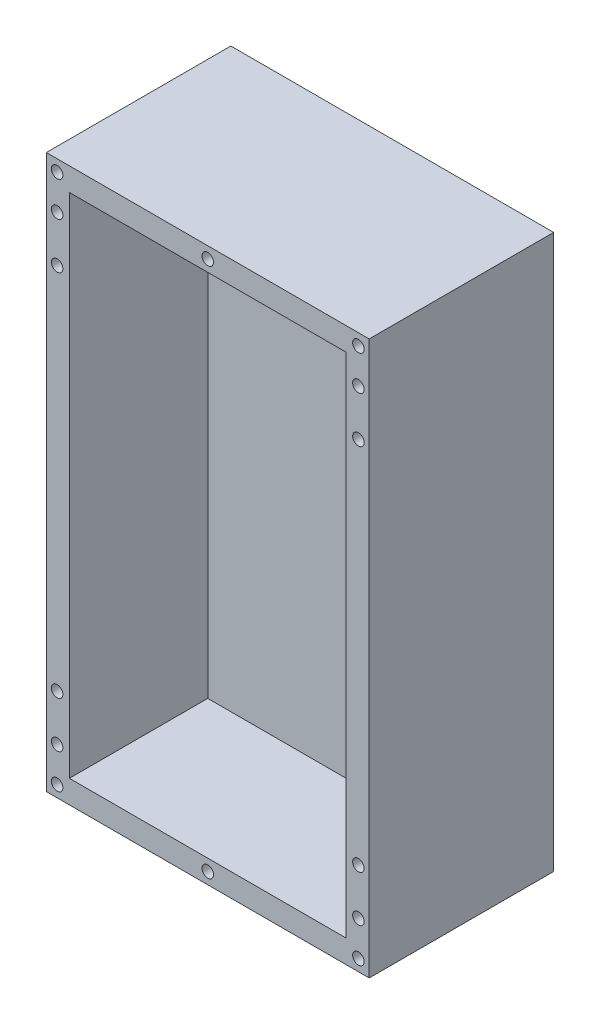
SolidWorks part; units mm, degrees
ref_plane "Front Plane" through (0, 0, 0) normal (0, 0, 1) x (1, 0, 0)
ref_plane "Top Plane" through (0, 0, 0) normal (0, 1, 0) x (1, 0, 0)
ref_plane "Right Plane" through (0, 0, 0) normal (1, 0, 0) x (0, 0, -1)
sketch "Sketch1" plane through (0, 0, 0) normal (0, 0, 1) x (1, 0, 0)
  line L0 (0, 609.6) -> (355.6, 0) construction
  line L1 (0, 609.6) -> (355.6, 609.6)
  line L2 (0, 609.6) -> (0, 0)
  line L3 (0, 0) -> (355.6, 0)
  line L4 (355.6, 609.6) -> (355.6, 0)
  line L5 (355.6, 609.6) -> (0, 0) construction
  line L9 (25.4, 584.2) -> (330.2, 584.2)
  line L10 (25.4, 584.2) -> (25.4, 25.4)
  line L11 (25.4, 25.4) -> (330.2, 25.4)
  line L12 (330.2, 584.2) -> (330.2, 25.4)
  line L13 (25.4, 584.2) -> (330.2, 25.4) construction
  line L14 (330.2, 584.2) -> (25.4, 25.4) construction
  point P12 (177.8, 304.8)
  point P13 (177.8, 304.8)
  dimension "D1" = 355.6
  dimension "D2" = 609.6
  dimension "D3" = 304.8
  dimension "D4" = 558.8
extrude "Boss-Extrude2" add sketch "Sketch1" along normal blind 203.2
ref_plane "Plane4" through (25.4, 584.2, 0) normal (0, -1, 0) x (-1, 0, 0)
sketch "Sketch4" plane through (0, 0, 0) normal (0, 0, -1) x (-1, 0, 0)
  line L1 (-330.2, 584.2) -> (-25.4, 584.2)
  line L2 (-330.2, 584.2) -> (-330.2, 25.4)
  line L3 (-330.2, 25.4) -> (-25.4, 25.4)
  line L4 (-25.4, 584.2) -> (-25.4, 25.4)
extrude "Boss-Extrude3" add sketch "Sketch4" against normal blind 50.8
sketch "Sketch5" plane through (0, 0, 203.2) normal (0, 0, 1) x (1, 0, 0)
  line L0 (177.8, 0) -> (177.8, 609.6) construction
  line L1 (0, 0) -> (355.6, 0) construction
  line L2 (355.6, 609.6) -> (0, 609.6) construction
  line L3 (355.6, 304.8) -> (0, 304.8) construction
  line L4 (355.6, 0) -> (355.6, 609.6) construction
  line L5 (0, 609.6) -> (0, 0) construction
  circle A0 centre (11.8857, 50.9474) radius 6.35
  circle A1 centre (11.8857, 101.7474) radius 6.35
  circle A2 centre (11.8857, 507.8526) radius 6.35
  circle A3 centre (11.8857, 558.6526) radius 6.35
  circle A4 centre (343.7143, 50.9474) radius 6.35
  circle A5 centre (343.7143, 101.7474) radius 6.35
  circle A6 centre (343.7143, 558.6526) radius 6.35
  circle A7 centre (343.7143, 507.8526) radius 6.35
  dimension "D1" = 12.7
  dimension "D2" = 50.8
extrude "Cut-Extrude1" cut sketch "Sketch5" against normal blind 25.4
sketch "Sketch6" plane through (0, 0, 203.2) normal (0, 0, 1) x (1, 0, 0)
  line L0 (0, 304.8) -> (355.6, 304.8) construction
  line L1 (0, 609.6) -> (0, 0) construction
  line L2 (355.6, 0) -> (355.6, 609.6) construction
  circle A0 centre (343.7143, 596.9) radius 6.35
  circle A1 centre (177.8, 596.9) radius 6.35
  circle A2 centre (11.8857, 596.9) radius 6.35
  circle A3 centre (343.7143, 12.7) radius 6.35
  circle A4 centre (177.8, 12.7) radius 6.35
  circle A5 centre (11.8857, 12.7) radius 6.35
extrude "Cut-Extrude2" cut sketch "Sketch6" against normal blind 12.7
